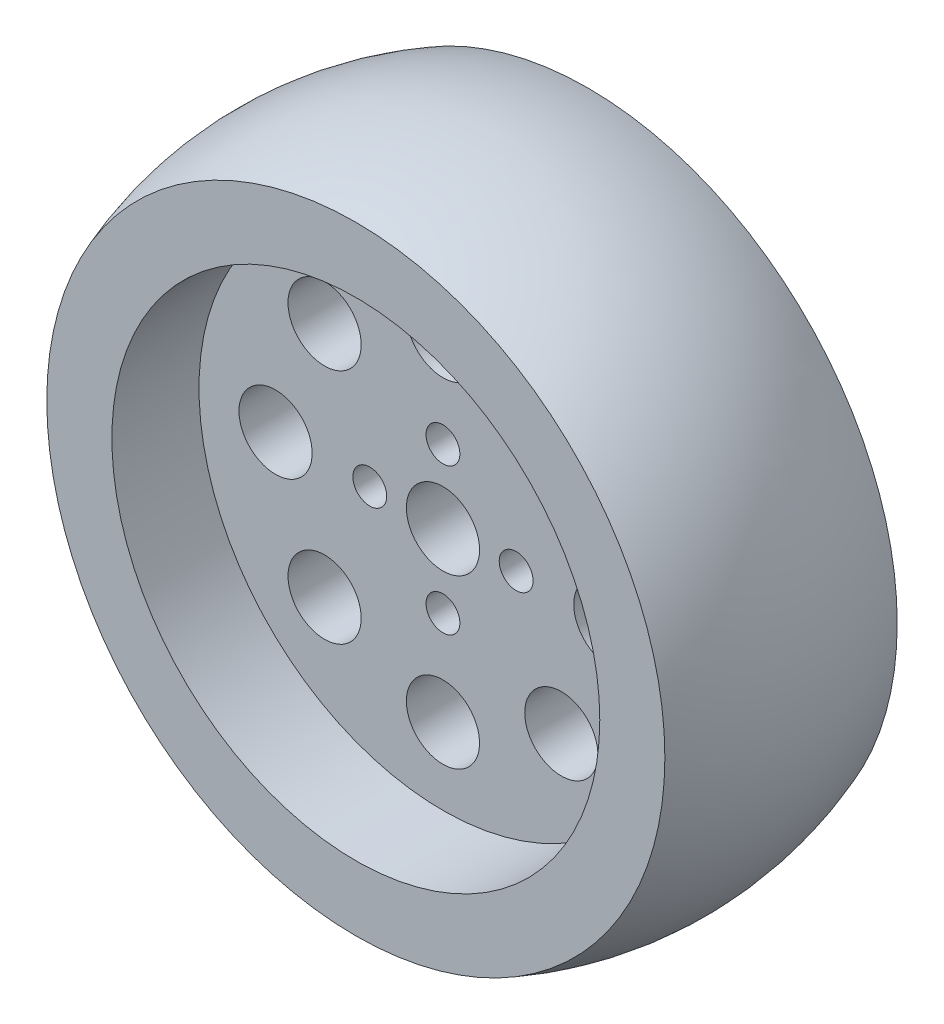
SolidWorks part; units mm, degrees
material "PE High Density"
ref_plane "Front Plane" through (0, 0, 0) normal (0, 0, 1) x (1, 0, 0)
ref_plane "Top Plane" through (0, 0, 0) normal (0, 1, 0) x (1, 0, 0)
ref_plane "Right Plane" through (0, 0, 0) normal (1, 0, 0) x (0, 0, -1)
sketch "Sketch1" plane through (0, 0, 0) normal (0, 1, 0) x (1, 0, 0)
  line L0 (33.7855, 12.7) -> (0, 12.7)
  line L1 (0, 12.7) -> (0, -12.7)
  line L2 (0, -12.7) -> (33.7855, -12.7)
  line L3 (0, 12.7) -> (0, -12.7) construction
  arc A0 (33.7855, -12.7) -> (33.7855, 12.7) centre (0.1, 0) ccw
revolve "Revolve1" add sketch "Sketch1" angle 360 about L3
sketch "Sketch2" plane through (0, 0, 0) normal (0, 1, 0) x (1, 0, 0)
  line L0 (26.67, 12.7) -> (0, 12.7)
  line L1 (0, 12.7) -> (0, -12.7)
  line L2 (0, -12.7) -> (26.67, -12.7)
  line L3 (26.67, -12.7) -> (26.67, -3.175)
  line L4 (26.67, -3.175) -> (4, -3.175)
  line L5 (4, -3.175) -> (4, 3.175)
  line L6 (4, 3.175) -> (26.67, 3.175)
  line L7 (26.67, 3.175) -> (26.67, 12.7)
  line L8 (0, 12.7) -> (0, -12.7) construction
revolve "Cut-Revolve1" cut sketch "Sketch2" angle 360 about L8
hole_wizard "Ø8.0 (8) Diameter Hole1" positions "Sketch4" profile "Sketch3" hole size "Ø8.0" standard "ANSI Metric"
sketch "Sketch4" plane through (0, 0, -3.175) normal (0, 0, -1) x (-1, 0, 0)
  point P0 (0, -18.3)
  point P1 (-12.9401, -12.9401)
  point P2 (-18.3, 0)
  point P3 (-12.9401, 12.9401)
  point P4 (0, 18.3)
  point P5 (12.9401, 12.9401)
  point P6 (18.3, 0)
  point P7 (12.9401, -12.9401)
sketch "Sketch3" plane through (0, -18.3, -3.175) normal (1, 0, 0) x (0, 1, 0)
  line L0 (0, 0) -> (0, 15.875)
  line L1 (0, 15.875) -> (4, 15.875)
  line L2 (4, 15.875) -> (4, 0)
  line L5 (4, 0) -> (0, 0)
  line L11 (0, -6.35) -> (0, 107.95) construction
  dimension "Thru Hole Dia." = 8
  dimension "Thru Hole Depth" = 15.875
hole_wizard "Ø3.7 (3.7) Diameter Hole1" positions "Sketch6" profile "Sketch5" hole size "Ø3.7" standard "ANSI Metric"
sketch "Sketch6" plane through (0, 0, -3.175) normal (0, 0, -1) x (-1, 0, 0)
  point P0 (-8, 0)
  point P1 (0, -8)
  point P2 (8, 0)
  point P3 (0, 8)
sketch "Sketch5" plane through (8, 0, -3.175) normal (1, 0, 0) x (0, 1, 0)
  line L0 (0, 0) -> (0, 15.875)
  line L1 (0, 15.875) -> (1.85, 15.875)
  line L2 (1.85, 15.875) -> (1.85, 0)
  line L5 (1.85, 0) -> (0, 0)
  line L11 (0, -6.35) -> (0, 107.95) construction
  dimension "Thru Hole Dia." = 3.7
  dimension "Thru Hole Depth" = 15.875
